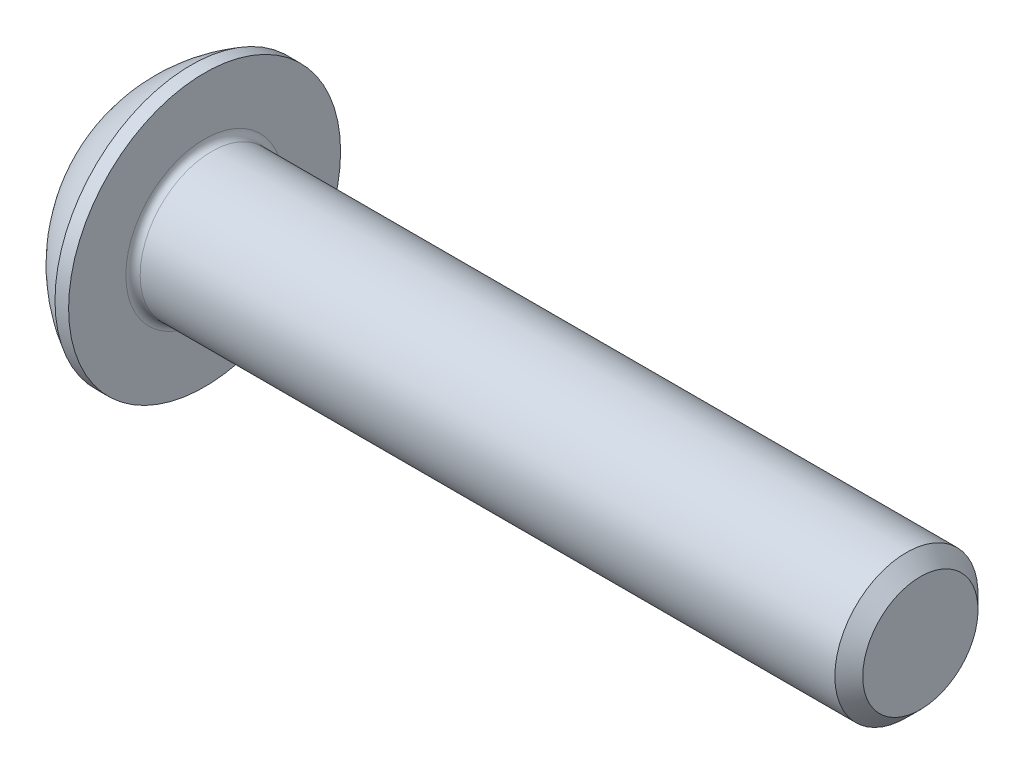
SolidWorks part; units mm, degrees
ref_plane "Plane1" through (0, 0, 0) normal (0, 0, 1) x (1, 0, 0)
ref_plane "Plane2" through (0, 0, 0) normal (0, 1, 0) x (1, 0, 0)
ref_plane "Plane3" through (0, 0, 0) normal (1, 0, 0) x (0, 0, -1)
sketch "BodySke" plane through (0, 0, 0) normal (0, 0, 1) x (1, 0, 0)
  line L0 (22.2, 0) -> (22.2, 1.61)
  line L1 (21.81, 2) -> (2.2, 2)
  line L2 (2.2, 2) -> (2.2, 3.8)
  line L3 (2.2, 3.8) -> (1.82, 3.8)
  line L4 (0, 0) -> (101.6, 0) construction
  line L5 (2.2, -3.8) -> (1.82, -3.8) construction
  line L6 (55.6768, -2) -> (2.2, -2) construction
  line L7 (22.2, 0) -> (0, 0)
  line L8 (0, 1.9) -> (0, -1.9) construction
  line L9 (0, 0) -> (0, 1.9)
  line L10 (22.2, 1.61) -> (21.81, 2)
  line L11 (22.2, -1.61) -> (21.81, -2) construction
  line L12 (2.9, 9.525) -> (2.9, -2) construction
  line L13 (2.2, 9.525) -> (2.2, -2) construction
  arc A1 (0, 1.9) -> (1.82, 3.8) centre (3.8853, 0) cw
  dimension "Head_side_ht" = 0.38
  dimension "Body_ch_ang" = 45
revolve "BaseBody" add sketch "BodySke" angle 360 about L4
cosmetic thread "ThreadCosmetic" [suppressed] parameters "Thread_length"=18.6, "Thread_minor"=3.22
fillet "Fillet1" radius 0.2 1 edges at (2.2, 0, 2)
sketch "Sketch2" plane through (0, 0, 0) normal (0, 0, 1) x (1, 0, 0)
  line L0 (0, 1.25) -> (1.3, 1.25)
  line L1 (1.3, 1.25) -> (2.0217, 0)
  line L3 (2.0217, 0) -> (0, 0)
  line L4 (0, 0) -> (0, 1.25)
  line L5 (0, -1.25) -> (1.3, -1.25) construction
  line L6 (0, 0) -> (47.625, 0) construction
  dimension "D2" = 60
  dimension "PreBroach_depth" = 1.3
  dimension "PreBroach_dia" = 2.5
revolve "PreBroach" cut sketch "Sketch2" angle 360 about L6
sketch "Sketch3" plane through (0, 0, 0) normal (1, 0, 0) x (0, 0, -1)
  line L0 (-1.25, -0.7217) -> (-1.25, 0.7217)
  line L1 (-1.25, 0.7217) -> (0, 1.4434)
  line L2 (0, 1.4434) -> (1.25, 0.7217)
  line L3 (1.25, 0.7217) -> (1.25, -0.7217)
  line L4 (1.25, -0.7217) -> (0, -1.4434)
  line L5 (0, -1.4434) -> (-1.25, -0.7217)
  dimension "Hex_size" = 2.5
  dimension "D3" = 2.5
  dimension "D1" = 1.25
  dimension "D2" = 1.25
extrude "Hex" cut sketch "Sketch3" along normal blind 1.3
sketch "ThdSchSke" plane through (0, 0, 0) normal (0, 0, 1) x (1, 0, 0)
  line L0 (3.6, -1.61) -> (3.3269, -2)
  line L1 (3.6, -1.61) -> (3.8731, -2)
  line L2 (3.8731, -2) -> (3.8731, -2.5)
  line L3 (-3.175, 0) -> (5.1513, 0) construction
  line L5 (3.8731, -2.5) -> (3.3269, -2.5)
  line L6 (3.3269, -2.5) -> (3.3269, -2)
  dimension "SideAngle" = 55
  dimension "VeeAngle" = 70
revolve "ThreadSchematic" [suppressed] cut sketch "ThdSchSke" angle 360 about L3
pattern_linear "ThdSchPat" [suppressed]
equation "\"D1@BodySke\" = \"Head_dia@BodySke\" * .5"
equation "\"Thread_minor@ThreadCosmetic\" = \"Minor_dia@BodySke\""
equation "\"D1@Sketch3\" = \"Hex_size@Sketch3\" / 2"
equation "\"D2@Sketch3\" = \"D1@Sketch3\""
equation "\"D3@Sketch3\" = \"Hex_size@Sketch3\""
equation "\"Thread_length@ThreadCosmetic\" = ((sgn( (\"Length@BodySke\" - \"Advance@BodySke\" * 2.0) - \"Thread_nom@BodySke\" )-1)*( (\"Length@BodySke\" - \"Advance@BodySke\" * 2.0) - \"Thread_nom@BodySke\" ))/-2+ \"Thread_nom@BodySke\""
equation "\"Thread_minor@ThdSchSke\" = \"Minor_dia@BodySke\""
equation "\"Diameter@ThdSchSke\" = \"Diameter@BodySke\""
equation "\"Overcut@ThdSchSke\" = \"Diameter@BodySke\" * 1.25"
equation "\"Start@ThdSchSke\" = \"Head_ht@BodySke\" + \"Length@BodySke\" - \"Thread_length@ThreadCosmetic\"  '---Non-countersunk---"
equation "\"Num_threads@ThdSchPat\" = int( \"Thread_length@ThreadCosmetic\" / \"Advance@BodySke\" + 0.999 )  + 1"
equation "\"Advance@ThdSchPat\" = \"Thread_length@ThreadCosmetic\" /  (\"Num_threads@ThdSchPat\" - 1) 'relax it"
equation "\"Num_threads@ThdSchPat\" = \"Num_threads@ThdSchPat\" - sgn( \"Num_threads@ThdSchPat\" - 1) '---chamfered tips only---"
